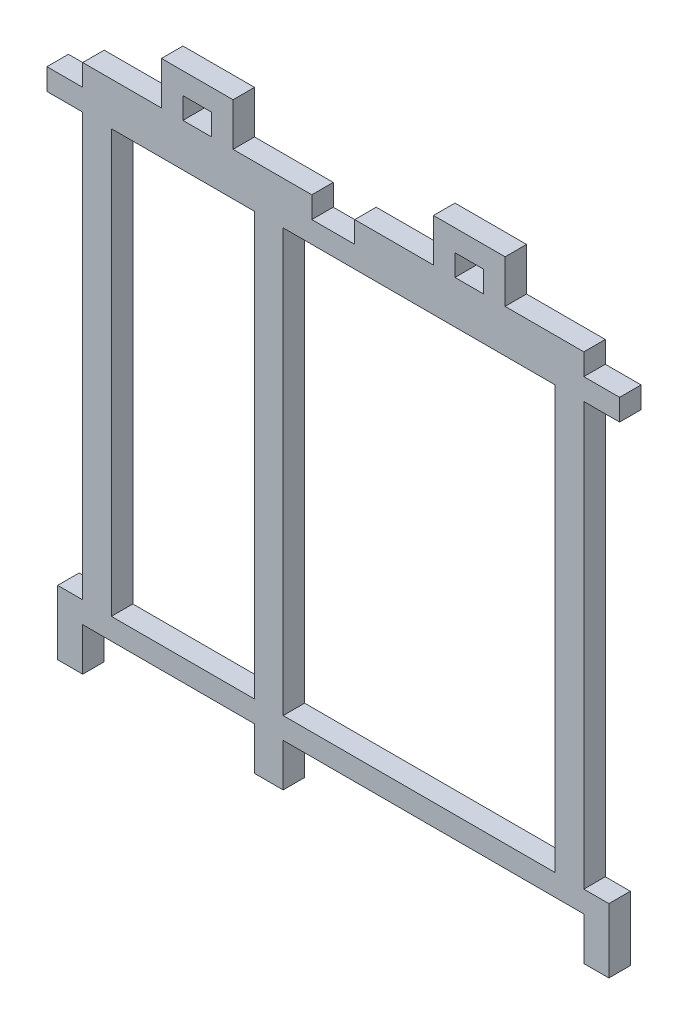
SolidWorks part; units mm, degrees
material "Custom Plastic"
ref_plane "Front Plane" through (0, 0, 0) normal (0, 0, 1) x (1, 0, 0)
ref_plane "Top Plane" through (0, 0, 0) normal (0, 1, 0) x (1, 0, 0)
ref_plane "Right Plane" through (0, 0, 0) normal (1, 0, 0) x (0, 0, -1)
sketch "Sketch1" plane through (0, 0, 0) normal (0, 0, 1) x (1, 0, 0)
  line L75 (5, -3) -> (0, -3)
  line L76 (0, -3) -> (0, 0)
  line L77 (0, 0) -> (5, 0)
  line L78 (5, 0) -> (5, 3)
  line L79 (5, 3) -> (37, 3)
  line L80 (37, 3) -> (37, 0)
  line L81 (37, 0) -> (43, 0)
  line L82 (43, 0) -> (43, 3)
  line L83 (43, 3) -> (75, 3)
  line L84 (75, 3) -> (75, 0)
  line L85 (75, 0) -> (80, 0)
  line L86 (80, 0) -> (80, -3)
  line L87 (80, -3) -> (75, -3)
  line L88 (75, -3) -> (75, -62)
  line L89 (75, -62) -> (78.5, -62)
  line L90 (78.5, -62) -> (78.5, -71)
  line L91 (78.5, -71) -> (75, -71)
  line L92 (75, -71) -> (75, -65)
  line L93 (75, -65) -> (33, -65)
  line L94 (33, -65) -> (33, -71)
  line L95 (33, -71) -> (29, -71)
  line L96 (29, -71) -> (29, -65)
  line L97 (29, -65) -> (5, -65)
  line L98 (5, -65) -> (5, -71)
  line L99 (5, -71) -> (1.5, -71)
  line L100 (1.5, -71) -> (1.5, -62)
  line L101 (1.5, -62) -> (5, -62)
  line L102 (5, -3) -> (5, -62)
  line L103 (9, -62) -> (29, -62)
  line L104 (29, -62) -> (29, -3)
  line L105 (29, -3) -> (9, -3)
  line L106 (9, -3) -> (9, -62)
  line L107 (33, -3) -> (33, -62)
  line L108 (33, -62) -> (71, -62)
  line L109 (71, -62) -> (71, -3)
  line L110 (71, -3) -> (33, -3)
  point P56 (76.75, -62)
  dimension "D4" = 59
  dimension "D13" = 6
  dimension "D14" = 3
  dimension "D15" = 3
  dimension "D16" = 32
  dimension "D17" = 32
  dimension "D18" = 5
  dimension "D19" = 5
  dimension "D20" = 59
  dimension "D21" = 9
  dimension "D22" = 3.5
  dimension "D23" = 3
  dimension "D24" = 42
  dimension "D25" = 4
  dimension "D26" = 24
  dimension "D27" = 3.5
  dimension "D28" = 9
  dimension "D29" = 4
  dimension "D30" = 4
  dimension "D31" = 20
extrude "Boss-Extrude1" add sketch "Sketch1" along normal blind 3
sketch "Sketch2" plane through (0, 0, 3) normal (0, 0, 1) x (1, 0, 0)
  line L0 (37, 3) -> (5, 3) construction
  line L1 (16, 3) -> (26, 3)
  line L2 (16, 3) -> (16, 9)
  line L3 (16, 9) -> (26, 9)
  line L4 (26, 3) -> (26, 9)
  line L5 (5, 3) -> (5, 0) construction
  line L6 (19, 3) -> (23, 3)
  line L7 (19, 3) -> (19, 6)
  line L8 (19, 6) -> (23, 6)
  line L9 (23, 3) -> (23, 6)
  line L10 (40, 0) -> (40, 10.82) construction
  line L11 (43, 0) -> (37, 0) construction
  line L12 (57, 3) -> (57, 6)
  line L13 (61, 6) -> (57, 6)
  line L14 (61, 3) -> (61, 6)
  line L15 (61, 3) -> (57, 3)
  line L16 (54, 3) -> (54, 9)
  line L17 (64, 9) -> (54, 9)
  line L18 (64, 3) -> (64, 9)
  line L19 (64, 3) -> (54, 3)
  line M28 (75, 3) -> (43, 3)
  line M32 (37, 3) -> (5, 3)
  dimension "D1" = 10
  dimension "D2" = 3
  dimension "D3" = 3
  dimension "D4" = 3
  dimension "D5" = 3
  dimension "D6" = 11
extrude "Boss-Extrude2" add sketch "Sketch2" against normal blind 3 contours L9 L4 L3 L2 L7 L8 M32 | L18 L17 L16 L12 L13 L14 M28
